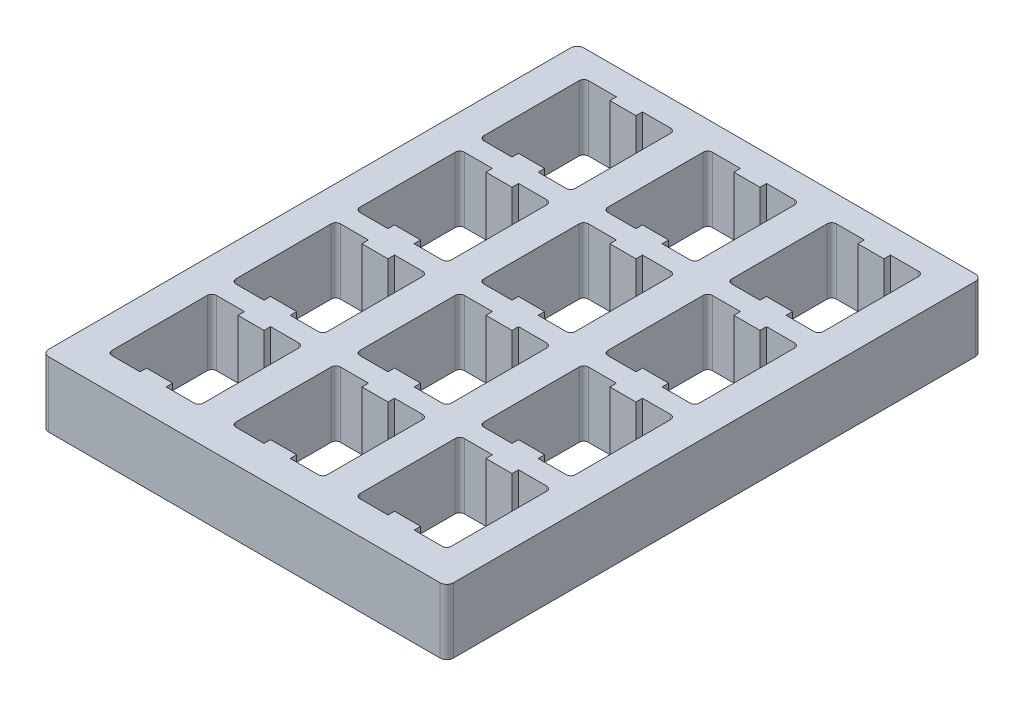
SolidWorks part; units mm, degrees
ref_plane "Front Plane" through (0, 0, 0) normal (0, 0, 1) x (1, 0, 0)
ref_plane "Top Plane" through (0, 0, 0) normal (0, 1, 0) x (1, 0, 0)
ref_plane "Right Plane" through (0, 0, 0) normal (1, 0, 0) x (0, 0, -1)
sketch "Sketch1" plane through (0, 0, 0) normal (0, 1, 0) x (1, 0, 0)
  line L1 (-31, -41) -> (31, -41)
  line L2 (-31, -41) -> (-31, 41)
  line L3 (-31, 41) -> (31, 41)
  line L4 (31, -41) -> (31, 41)
  line L5 (-31, -41) -> (31, 41) construction
  line L6 (-31, 41) -> (31, -41) construction
  point P0 (0, 0)
  dimension "D1" = 62
  dimension "D2" = 82
extrude "Boss-Extrude1" add sketch "Sketch1" along normal blind 10
fillet "Fillet1" radius 1 4 edges at (31, 5, -41) (-31, 5, -41) (-31, 5, 41) (31, 5, 41)
sketch "Sketch2" plane through (0, 10, 0) normal (0, 1, 0) x (1, 0, 0)
  line L0 (0, 41) -> (0, -41) construction
  line L1 (30, 41) -> (-30, 41) construction
  line L2 (-30, -41) -> (30, -41) construction
  line L6 (2, 21) -> (2, 22)
  line L7 (-6.3, 37) -> (-2, 37)
  line L8 (-7, 36.3) -> (-7, 21.7)
  line L9 (-6.3, 21) -> (-2, 21)
  line L10 (7, 36.3) -> (7, 21.7)
  line L11 (-7, 37) -> (7, 21) construction
  line L12 (-7, 21) -> (7, 37) construction
  line L19 (2, 22) -> (-2, 22)
  line L20 (-2, 22) -> (-2, 21)
  line L21 (2, 37) -> (2, 36)
  line L22 (2, 36) -> (-2, 36)
  line L23 (-2, 36) -> (-2, 37)
  line L24 (2, 37) -> (6.3, 37)
  line L25 (2, 21) -> (6.3, 21)
  arc A0 (6.3, 21) -> (7, 21.7) centre (6.3, 21.7) ccw
  arc A1 (7, 36.3) -> (6.3, 37) centre (6.3, 36.3) ccw
  arc A2 (-6.3, 37) -> (-7, 36.3) centre (-6.3, 36.3) ccw
  arc A3 (-7, 21.7) -> (-6.3, 21) centre (-6.3, 21.7) ccw
  point P12 (0, 29)
  dimension "D1" = 16
  dimension "D2" = 14
  dimension "D3" = 4
  dimension "D4" = 1
  dimension "D5" = 1
  dimension "D6" = 4
  dimension "D7" = 4
extrude "Cut-Extrude2" cut sketch "Sketch2" against normal blind 10 contours L10 A0 L25 L6 L19 L20 L9 A3 L8 A2 L7 L23 L22 L21 L24 A1
pattern_linear "LPattern1" count 4 spacing 19 along (0, 0, 1) of "Cut-Extrude2"
pattern_linear "LPattern3" count 2 spacing 19 along (-1, 0, 0) of "LPattern1", "Cut-Extrude2"
pattern_linear "LPattern4" count 2 spacing 19 along (1, 0, 0) of "LPattern1", "Cut-Extrude2"
